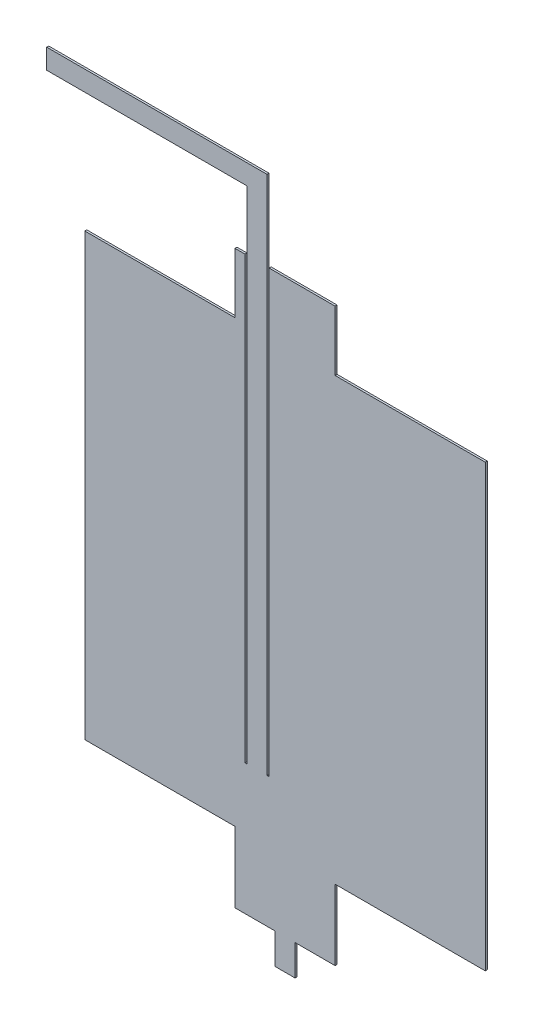
SolidWorks part; units mm, degrees
ref_plane "Front Plane" through (0, 0, 0) normal (0, 0, 1) x (1, 0, 0)
ref_plane "Top Plane" through (0, 0, 0) normal (0, 1, 0) x (1, 0, 0)
ref_plane "Right Plane" through (0, 0, 0) normal (1, 0, 0) x (0, 0, -1)
sketch "Sketch2" plane through (0, 0, 0) normal (0, 0, 1) x (1, 0, 0)
  line L0 (75, -55.233) -> (95, -55.233)
  line L2 (0, 0) -> (0, 200)
  line L3 (0, 200) -> (200, 200) construction
  line L4 (200, 0) -> (200, 200)
  line L6 (0, 0) -> (0, -20)
  line L8 (200, 0) -> (200, -20)
  line L9 (0, -20) -> (75, -20)
  line L10 (75, -20) -> (75, -55.233)
  line L12 (125, -55.233) -> (125, -20)
  line L13 (125, -20) -> (200, -20)
  line L14 (95, -55.233) -> (95, -70.5774)
  line L15 (95, -70.5774) -> (105, -70.5774)
  line L16 (105, -70.5774) -> (105, -55.233)
  line L17 (105, -55.233) -> (125, -55.233)
  line L18 (75, 200) -> (75, 230)
  line L19 (92, 230) -> (125, 230)
  line L20 (125, 230) -> (125, 200)
  line L21 (81, 230) -> (81, 10)
  line L22 (81, 10) -> (91, 10) construction
  line L23 (91, 10) -> (91, 230)
  line L24 (81, 230) -> (81, 260)
  line L25 (81, 260) -> (-19, 260)
  line L26 (-19, 260) -> (-19, 270)
  line L27 (-19, 270) -> (91, 270)
  line L28 (91, 270) -> (91, 230)
  line L29 (75, 230) -> (80, 230)
  line L30 (80, 10) -> (81, 10)
  line L31 (0, 200) -> (75, 200)
  line L32 (125, 200) -> (200, 200)
  line L33 (80, 230) -> (80, 10)
  line L34 (92, 10) -> (92, 230)
  line L35 (91, 10) -> (92, 10)
  line L36 (0, 0) -> (200, 0)
  dimension "D1" = 200
  dimension "D2" = 200
  dimension "D3" = 20
  dimension "D4" = 75
  dimension "D5" = 75
  dimension "D6" = 20
  dimension "D7" = 20
  dimension "D8" = 10
  dimension "D9" = 30
  dimension "D10" = 10
  dimension "D11" = 6
  dimension "D14" = 10
  dimension "D15" = 100
  dimension "D16" = 1
extrude "Boss-Extrude1" add sketch "Sketch2" along normal blind 1 contours L2 L31 L18 L29 L33 L30 L21 L24 L25 L26 L27 L28 L23 L35 L34 L19 L20 L32 L4 L8 L13 L12 L17 L16 L15 L14 L0 L10 L9 L6
